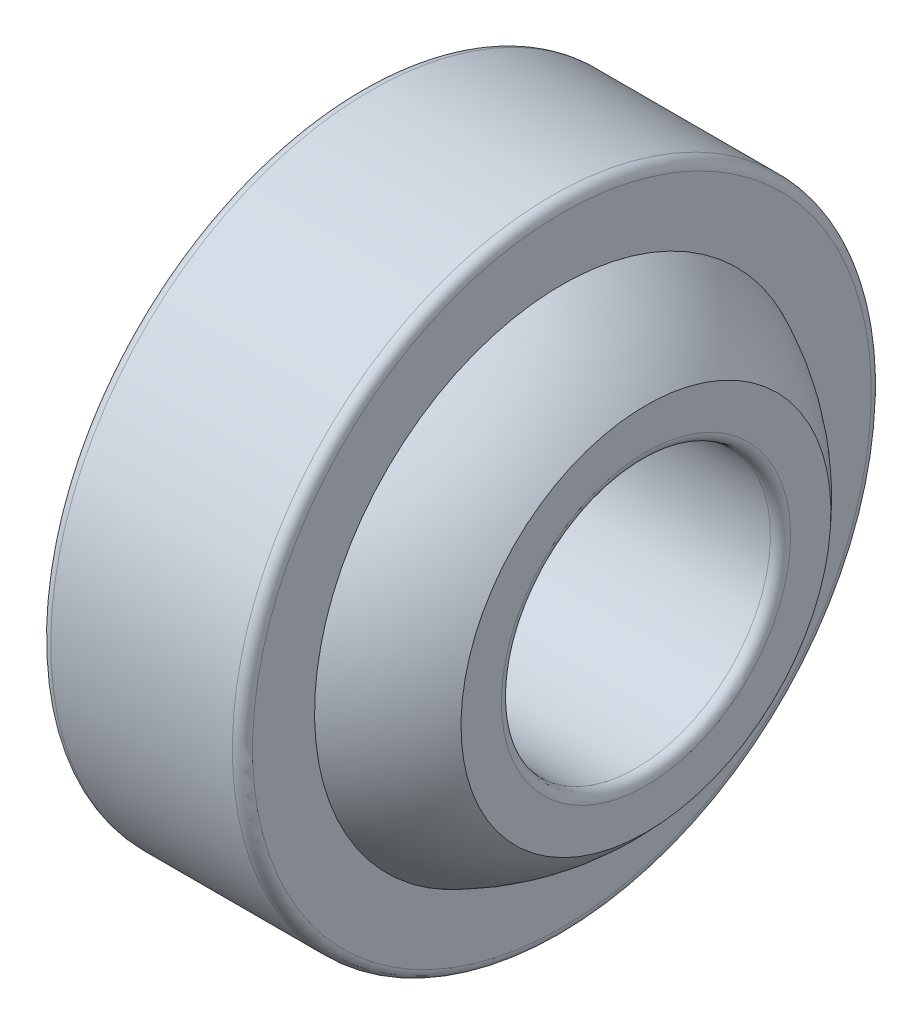
SolidWorks part; units mm, degrees
ref_plane "前视基准面" through (0, 0, 0) normal (0, 0, 1) x (1, 0, 0)
ref_plane "上视基准面" through (0, 0, 0) normal (0, 1, 0) x (1, 0, 0)
ref_plane "右视基准面" through (0, 0, 0) normal (1, 0, 0) x (0, 0, -1)
sketch "尺寸草图" plane through (0, 0, 0) normal (0, 0, 1) x (1, 0, 0)
  line L0 (0, 9.5) -> (0, 0) construction
  line L1 (-7, 0) -> (7, 0) construction
  line L2 (-5.2, 4) -> (5.2, 4)
  line L5 (-3, 7.3551) -> (-3, 9.2)
  line L6 (-2.7, 9.5) -> (2.7, 9.5)
  line L7 (3, 9.2) -> (3, 7.3551)
  line L10 (-5.5, 5.5) -> (-5.5, 4.3)
  line L11 (5.5, 5.5) -> (5.5, 4.3)
  arc A1 (-5.5, 5.5) -> (5.5, 5.5) centre (0, 0.7) cw
  arc A2 (-3, 9.2) -> (-2.7, 9.5) centre (-2.7, 9.2) cw
  arc A3 (2.7, 9.5) -> (3, 9.2) centre (2.7, 9.2) cw
  arc A4 (5.2, 4) -> (5.5, 4.3) centre (5.2, 4.3) ccw
  arc A5 (-5.5, 4.3) -> (-5.2, 4) centre (-5.2, 4.3) ccw
  dimension "dk" = 16
  dimension "r1s" = 0.3
  dimension "rs" = 0.3
  dimension "C" = 6
  dimension "D" = 19
  dimension "d_" = 8
  dimension "d1" = 11
  dimension "B" = 11
sketch "草图2" plane through (0, 0, 0) normal (0, 0, 1) x (1, 0, 0)
  line L11 (-3, 7.3551) -> (-3, 9.2) construction
  line L12 (-2.7, 9.5) -> (2.7, 9.5) construction
  line L13 (3, 9.2) -> (3, 7.3551) construction
  line L15 (-3, 7.3551) -> (-3, 9.2)
  line L16 (-2.7, 9.5) -> (2.7, 9.5)
  line L17 (3, 9.2) -> (3, 7.3551)
  arc A0 (5.5, 5.5) -> (-5.5, 5.5) centre (0, 0.7) ccw construction
  arc A1 (-2.7, 9.5) -> (-3, 9.2) centre (-2.7, 9.2) ccw construction
  arc A2 (3, 7.3551) -> (-3, 7.3551) centre (0, 0.7) ccw
  arc A3 (3, 9.2) -> (2.7, 9.5) centre (2.7, 9.2) ccw construction
  arc A4 (-2.7, 9.5) -> (-3, 9.2) centre (-2.7, 9.2) ccw
  arc A5 (3, 9.2) -> (2.7, 9.5) centre (2.7, 9.2) ccw
revolve "旋转1" add sketch "草图2" angle 360 about L1
sketch "草图3" plane through (0, 0, 0) normal (0, 0, 1) x (1, 0, 0)
  line L0 (-5.5, 5.5) -> (-5.5, 4.3) construction
  line L2 (-5.2, 4) -> (5.2, 4) construction
  line L4 (5.5, 5.5) -> (5.5, 4.3) construction
  line L5 (-5.5, 5.5) -> (-5.5, 4.3)
  line L7 (-5.2, 4) -> (5.2, 4)
  line L9 (5.5, 5.5) -> (5.5, 4.3)
  arc A0 (5.5, 5.5) -> (-5.5, 5.5) centre (0, 0.7) ccw construction
  arc A1 (5.5, 5.5) -> (-5.5, 5.5) centre (0, 0.7) ccw
  arc A2 (5.2, 4) -> (5.5, 4.3) centre (5.2, 4.3) ccw construction
  arc A3 (-5.5, 4.3) -> (-5.2, 4) centre (-5.2, 4.3) ccw construction
  arc A4 (5.2, 4) -> (5.5, 4.3) centre (5.2, 4.3) ccw
  arc A5 (-5.5, 4.3) -> (-5.2, 4) centre (-5.2, 4.3) ccw
revolve "旋转2" add sketch "草图3" angle 360 about L1
